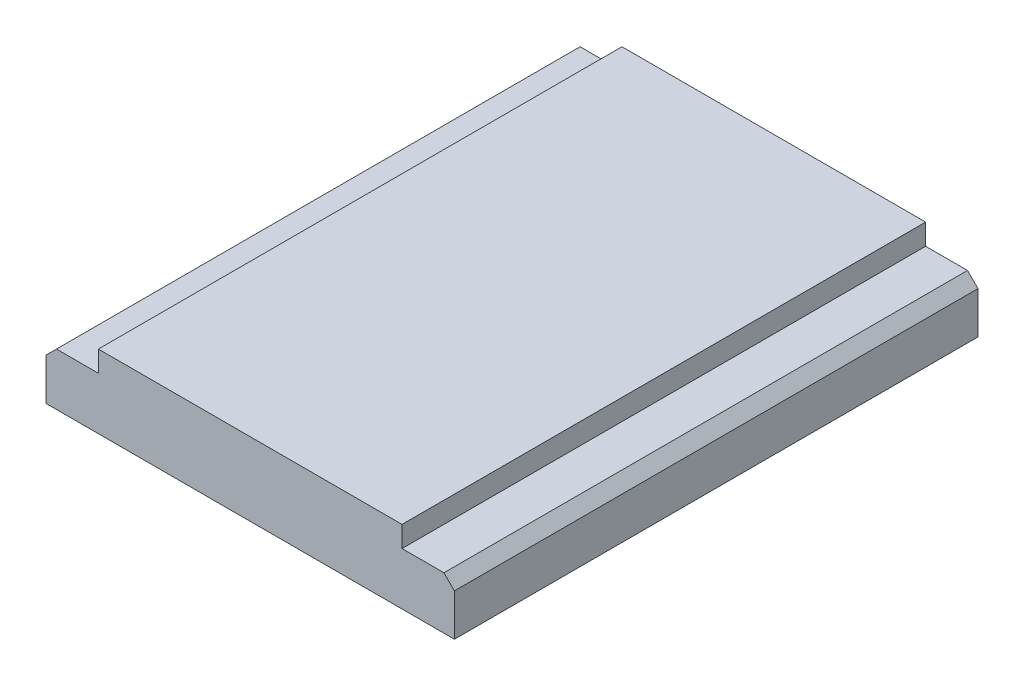
SolidWorks part; units mm, degrees
ref_plane "Front Plane" through (0, 0, 0) normal (0, 0, 1) x (1, 0, 0)
ref_plane "Top Plane" through (0, 0, 0) normal (0, 1, 0) x (1, 0, 0)
ref_plane "Right Plane" through (0, 0, 0) normal (1, 0, 0) x (0, 0, -1)
sketch "Sketch1" plane through (0, 0, 0) normal (0, 0, 1) x (1, 0, 0)
  line L0 (0, 0) -> (7.8, 0)
  line L1 (7.8, 0) -> (7.8, 1)
  line L2 (7.8, 1) -> (6.8, 1)
  line L3 (6.8, 1) -> (6.8, 1.4)
  line L4 (6.8, 1.4) -> (1, 1.4)
  line L5 (1, 1.4) -> (1, 1)
  line L6 (1, 1) -> (0, 1)
  line L7 (0, 1) -> (0, 0)
  dimension "D1" = 7.8
  dimension "D2" = 1
  dimension "D3" = 1
  dimension "D4" = 1
  dimension "D5" = 0.4
extrude "Boss-Extrude1" add sketch "Sketch1" along normal blind 10
chamfer "Chamfer1" distance 0.2 angle 45 2 edges at (0, 1, 5) (7.8, 1, 5)
